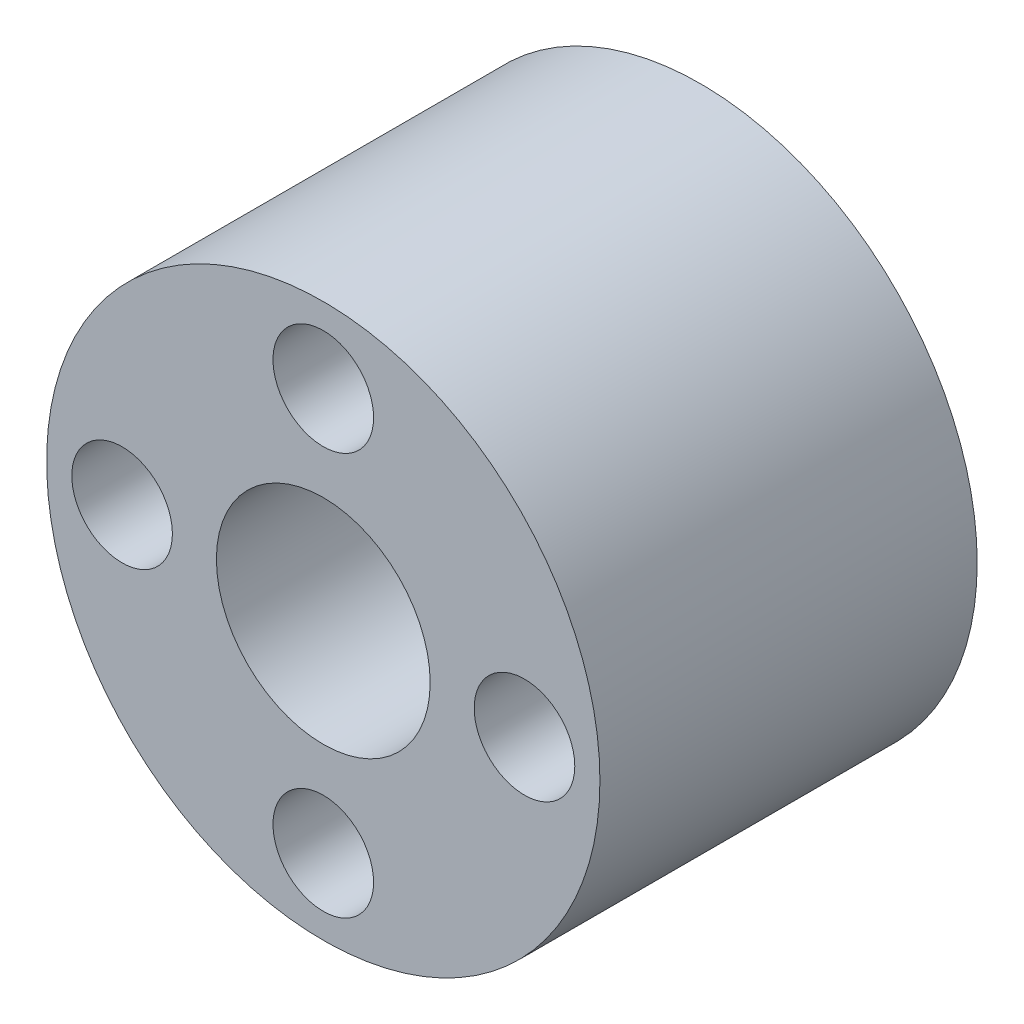
SolidWorks part; units mm, degrees
material "Plain Carbon Steel"
ref_plane "Front Plane" through (0, 0, 0) normal (0, 0, 1) x (1, 0, 0)
ref_plane "Top Plane" through (0, 0, 0) normal (0, 1, 0) x (1, 0, 0)
ref_plane "Right Plane" through (0, 0, 0) normal (1, 0, 0) x (0, 0, -1)
sketch "Sketch1" plane through (0, 0, 0) normal (0, 0, 1) x (1, 0, 0)
  circle A0 centre (0, 0) radius 11
  circle A1 centre (0, 0) radius 8 construction
  circle A2 centre (0, 8) radius 2
  circle A3 centre (8, 0) radius 2
  circle A4 centre (0, -8) radius 2
  circle A5 centre (-8, 0) radius 2
  point P15 (0, 0)
  dimension "D1" = 4
extrude "Boss-Extrude1" add sketch "Sketch1" along normal blind 15 contours A0 A5 A4 A3 A2
sketch "Sketch3" plane through (0, 0, 15) normal (0, 0, 1) x (1, 0, 0)
  circle A0 centre (0, 0) radius 8 construction
  circle A1 centre (0, 8) radius 2
  circle A2 centre (8, 0) radius 2
  circle A3 centre (0, -8) radius 2
  circle A4 centre (-8, 0) radius 2
  point P14 (0, 0)
  dimension "D1" = 4
extrude "Cut-Extrude1" cut sketch "Sketch3" against normal blind 15 contours A4 | A1 | A2 | A3
sketch "Sketch4" plane through (0, 0, 15) normal (0, 0, 1) x (1, 0, 0)
  circle A0 centre (0, 0) radius 4.25
extrude "Cut-Extrude2" cut sketch "Sketch4" against normal blind 10
